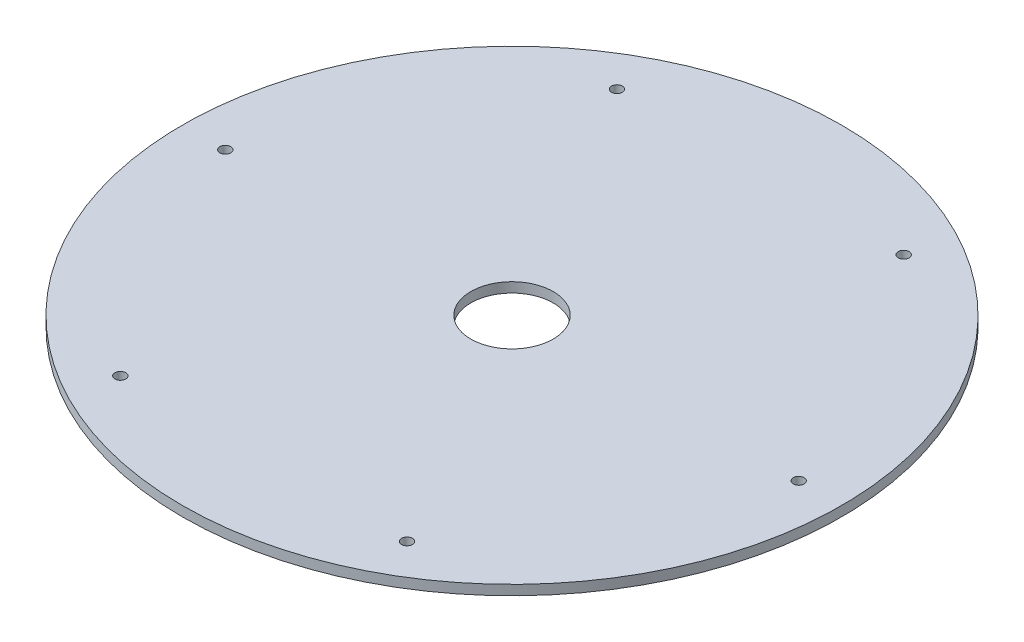
SolidWorks part; units mm, degrees
ref_plane "Front Plane" through (0, 0, 0) normal (0, 0, 1) x (1, 0, 0)
ref_plane "Top Plane" through (0, 0, 0) normal (0, 1, 0) x (1, 0, 0)
ref_plane "Right Plane" through (0, 0, 0) normal (1, 0, 0) x (0, 0, -1)
sketch "Sketch1" plane through (0, 0, 0) normal (0, 1, 0) x (1, 0, 0)
  line L0 (0, 0) -> (-100, 0) construction
  line L1 (0, 0) -> (-87, 0) construction
  circle A0 centre (0, 0) radius 100
  circle A1 centre (-87, 0) radius 1.65
  circle A2 centre (-43.5, 75.3442) radius 1.65
  circle A3 centre (43.5, 75.3442) radius 1.65
  circle A4 centre (87, 0) radius 1.65
  circle A5 centre (43.5, -75.3442) radius 1.65
  circle A6 centre (-43.5, -75.3442) radius 1.65
  dimension "D1" = 200
  dimension "D2" = 3.3
  dimension "D5" = 87
  dimension "D4" = 6
extrude "Boss-Extrude1" add sketch "Sketch1" along normal blind 3
sketch "Sketch2" plane through (0, 3, 0) normal (0, 1, 0) x (1, 0, 0)
  circle A0 centre (0, 0) radius 12.5
  dimension "D1" = 25
extrude "Cut-Extrude1" cut sketch "Sketch2" against normal through all
